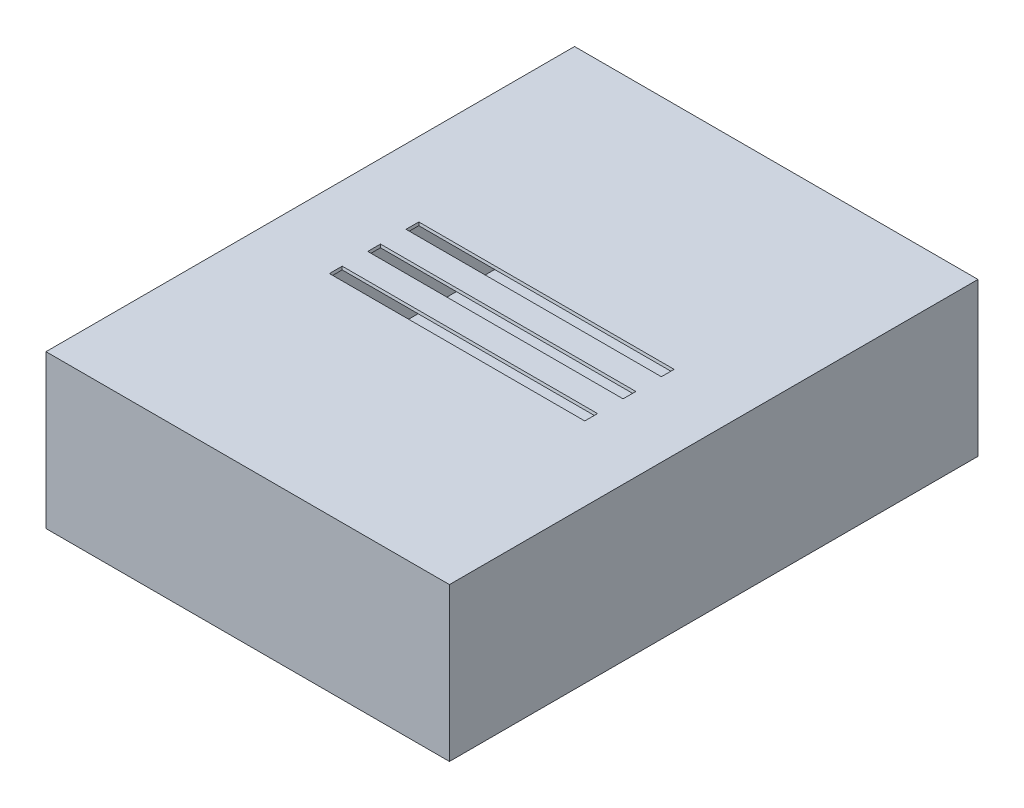
SolidWorks part; units mm, degrees
ref_plane "Front Plane" through (0, 0, 0) normal (0, 0, 1) x (1, 0, 0)
ref_plane "Wall Plane" through (0, 0, 0) normal (0, 1, 0) x (1, 0, 0)
ref_plane "Right Plane" through (0, 0, 0) normal (1, 0, 0) x (0, 0, -1)
sketch "Sketch2" plane through (0, 0, 0) normal (0, 0, 1) x (1, 0, 0)
  line L1 (0, 0) -> (401.32, 0)
  line L2 (0, 0) -> (0, 152.4)
  line L3 (0, 152.4) -> (401.32, 152.4)
  line L4 (401.32, 0) -> (401.32, 152.4)
  dimension "D1" = 152.4
  dimension "D2" = 401.32
extrude "Boss-Extrude1" add sketch "Sketch2" along normal blind 525.78
sketch "Sketch3" plane through (0, 152.4, 0) normal (0, 1, 0) x (1, 0, 0)
  line L0 (401.32, 0) -> (0, 0) construction
  line L1 (2.54, -523.24) -> (398.78, -523.24)
  line L2 (2.54, -523.24) -> (2.54, -25.4)
  line L3 (2.54, -25.4) -> (398.78, -25.4)
  line L4 (398.78, -523.24) -> (398.78, -25.4)
  line L5 (401.32, -525.78) -> (0, -525.78) construction
  line L6 (401.32, -525.78) -> (401.32, 0) construction
  line L7 (0, -525.78) -> (0, 0) construction
  dimension "D1" = 25.4
  dimension "D2" = 2.54
  dimension "D3" = 2.54
  dimension "D4" = 2.54
extrude "Cut-Extrude1" cut sketch "Sketch3" against normal blind 149.86 contours L3 L4 L1 L2
sketch "Sketch4" plane through (0, 152.4, 0) normal (0, 1, 0) x (1, 0, 0)
  line L1 (2.54, -25.4) -> (398.78, -25.4)
  line L2 (2.54, -25.4) -> (2.54, -523.24)
  line L3 (2.54, -523.24) -> (398.78, -523.24)
  line L4 (398.78, -25.4) -> (398.78, -523.24)
extrude "Boss-Extrude3" add sketch "Sketch4" against normal blind 2.54 contours L1 L4 L3 L2
sketch "Sketch8" plane through (0, 152.4, 0) normal (0, 1, 0) x (1, 0, 0)
  line L0 (73.66, -279.4) -> (327.66, -279.4)
  line L13 (73.66, -241.3) -> (327.66, -241.3)
  line L14 (73.66, -241.3) -> (73.66, -228.6)
  line L15 (73.66, -228.6) -> (327.66, -228.6)
  line L16 (327.66, -241.3) -> (327.66, -228.6)
  line L25 (73.66, -279.4) -> (73.66, -266.7)
  line L26 (73.66, -266.7) -> (327.66, -266.7)
  line L27 (327.66, -279.4) -> (327.66, -266.7)
  line L28 (73.66, -317.5) -> (327.66, -317.5)
  line L29 (73.66, -317.5) -> (73.66, -304.8)
  line L30 (73.66, -304.8) -> (327.66, -304.8)
  line L31 (327.66, -317.5) -> (327.66, -304.8)
  line L33 (0, -525.78) -> (0, 0) construction
  line L36 (401.32, 0) -> (0, 0) construction
  dimension "D1" = 254
  dimension "D2" = 12.7
  dimension "D3" = 73.66
  dimension "D4" = 73.66
  dimension "D5" = 73.66
  dimension "D6" = 25.4
  dimension "D7" = 25.4
  dimension "D8" = 12.7
  dimension "D9" = 12.7
  dimension "10" = 228.6
extrude "Cut-Extrude2" cut sketch "Sketch8" against normal blind 2.54 draft 15
